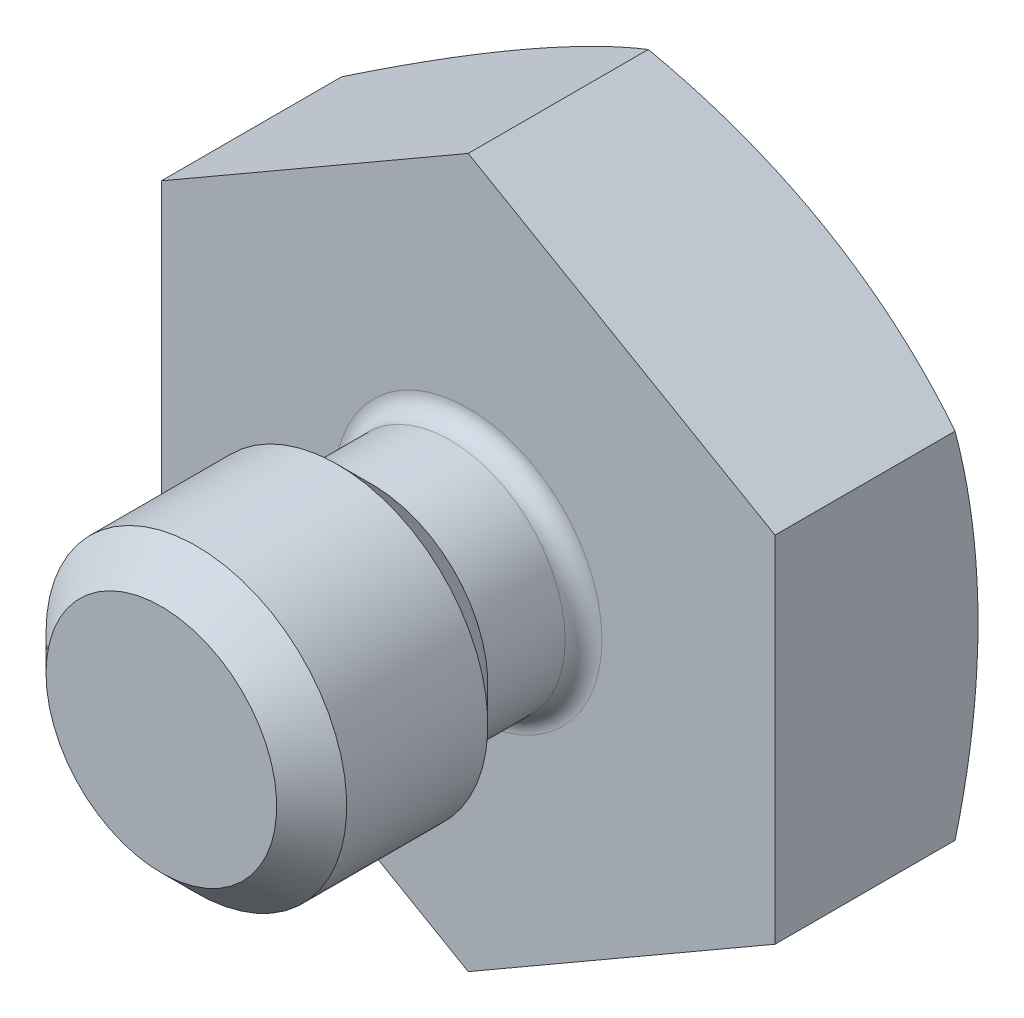
SolidWorks part; units mm, degrees
material "Alloy Steel"
ref_plane "Front Plane" through (0, 0, 0) normal (0, 0, 1) x (1, 0, 0)
ref_plane "Top Plane" through (0, 0, 0) normal (0, 1, 0) x (1, 0, 0)
ref_plane "Right Plane" through (0, 0, 0) normal (1, 0, 0) x (0, 0, -1)
sketch "Sketch1" plane through (0, 0, 0) normal (1, 0, 0) x (0, 0, -1)
  line L0 (0, 0) -> (-83.4165, 0) construction
  line L1 (0, 11.9891) -> (0, 2.3876)
  line L2 (0, 2.3876) -> (-1.9812, 2.3876)
  line L3 (-1.9812, 2.3876) -> (-2.7051, 3.1115)
  line L4 (-2.7051, 3.1115) -> (-5.6261, 3.1115)
  line L5 (-5.6261, 3.1115) -> (-6.35, 2.3876)
  line L6 (-6.35, 2.3876) -> (-6.35, 0)
  line L7 (-6.35, 0) -> (5.5372, 0)
  arc A1 (5.5372, 0) -> (0, 11.9891) centre (-10.2108, 0) ccw
  dimension "D1" = 5.5372
  dimension "D6" = 15.748
  dimension "D2" = 6.223
  dimension "D3" = 45
  dimension "D4" = 4.7752
  dimension "D5" = 1.9812
  dimension "D8" = 6.35
revolve "Revolve1" add sketch "Sketch1" angle 360 about L0
sketch "Sketch2" plane through (0, 0, 0) normal (0, 0, 1) x (1, 0, 0)
  line L1 (0, 7.3323) -> (-6.35, 3.6662)
  line L2 (-6.35, 3.6662) -> (-6.35, -3.6662)
  line L3 (-6.35, -3.6662) -> (0, -7.3323)
  line L4 (0, -7.3323) -> (6.35, -3.6662)
  line L5 (6.35, -3.6662) -> (6.35, 3.6662)
  line L6 (6.35, 3.6662) -> (0, 7.3323)
  circle A0 centre (0, 0) radius 6.35 construction
  dimension "D1" = 12.7
extrude "Cut-Extrude1" cut sketch "Sketch2" against normal through all flip side to cut
fillet "Fillet1" radius 0.381 1 edges at (-2.3876, 0, 0)
